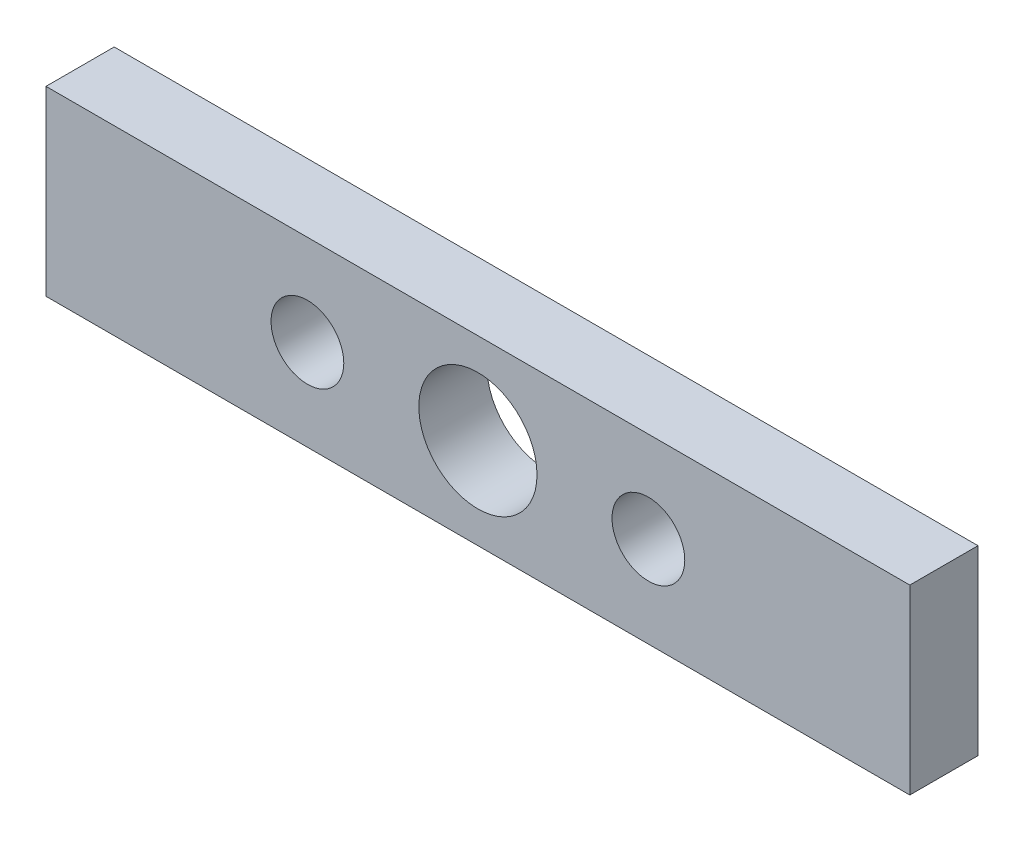
SolidWorks part; units mm, degrees
material "Oak"
ref_plane "Front Plane" through (0, 0, 0) normal (0, 0, 1) x (1, 0, 0)
ref_plane "Top Plane" through (0, 0, 0) normal (0, 1, 0) x (1, 0, 0)
ref_plane "Right Plane" through (0, 0, 0) normal (1, 0, 0) x (0, 0, -1)
sketch "Sketch1" plane through (0, 0, 0) normal (0, 0, 1) x (1, 0, 0)
  line L0 (-7.5, 0) -> (7.5, 0) construction
  line L1 (19, -4) -> (-19, -4)
  line L2 (19, -4) -> (19, 4)
  line L3 (19, 4) -> (-19, 4)
  line L4 (-19, -4) -> (-19, 4)
  line L5 (19, -4) -> (-19, 4) construction
  line L6 (19, 4) -> (-19, -4) construction
  circle A0 centre (0, 0) radius 2.6
  circle A1 centre (-7.5, 0) radius 1.6
  circle A2 centre (7.5, 0) radius 1.6
  point P0 (0, 0)
  dimension "D1" = 5.2
  dimension "D3" = 3.2
  dimension "D2" = 15
  dimension "D4" = 8
  dimension "D5" = 38
extrude "Boss-Extrude1" add sketch "Sketch1" along normal blind 3
